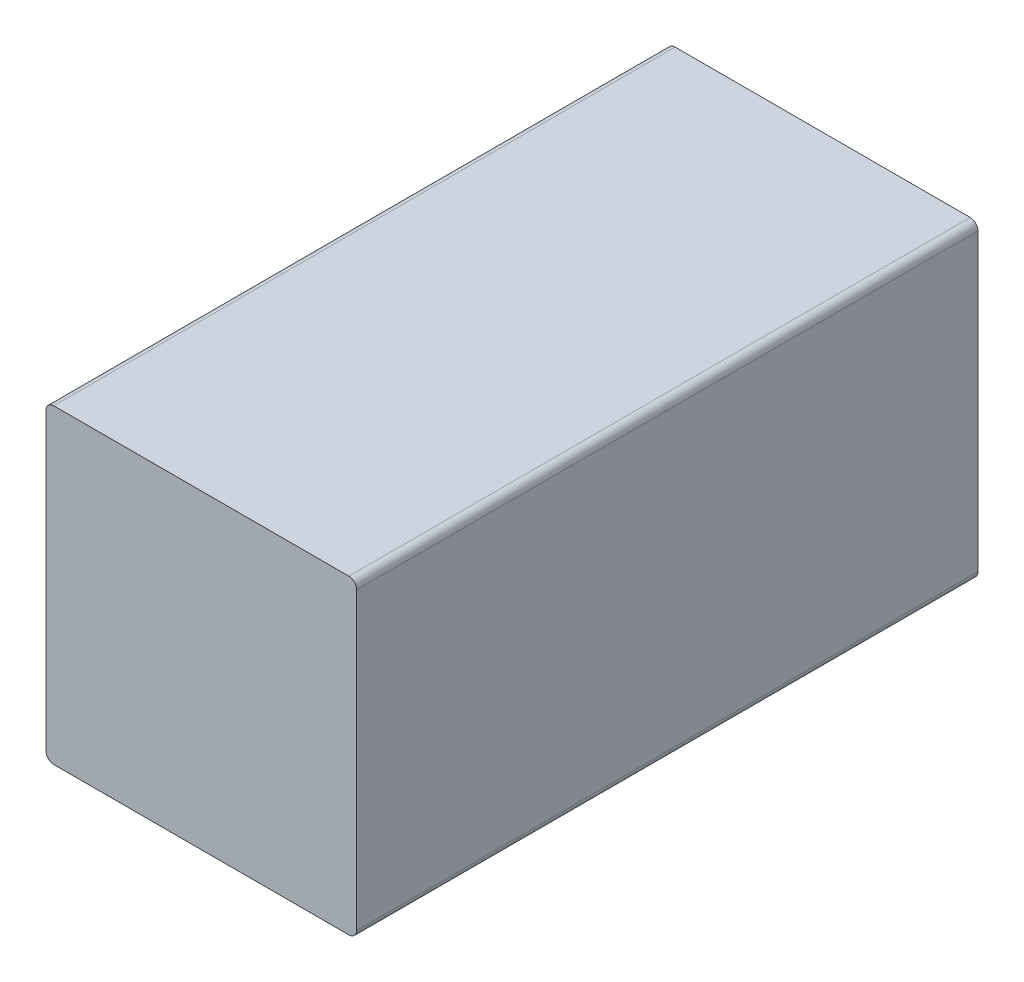
SolidWorks part; units mm, degrees
ref_plane "Front Plane" through (0, 0, 0) normal (0, 0, 1) x (1, 0, 0)
ref_plane "Top Plane" through (0, 0, 0) normal (0, 1, 0) x (1, 0, 0)
ref_plane "Right Plane" through (0, 0, 0) normal (1, 0, 0) x (0, 0, -1)
sketch "Sketch1" plane through (0, 0, 0) normal (1, 0, 0) x (0, 0, -1)
  line L0 (-4.7625, 2.3813) -> (4.7625, 2.3813)
  line L1 (-4.7625, 2.3813) -> (-4.7625, -2.3813) construction
  line L2 (0, 2.3813) -> (0, -2.3813) construction
  point P3 (-4.7625, 0)
  point P5 (0, 2.3813)
  point P6 (-7.1438, 2.3813)
  point P9 (7.1438, 2.3813)
  dimension "Length" = 9.525
  dimension "Height" = 4.7625
  dimension "D1" = 11.9062
sketch "Sketch2" plane through (0, 0, 0) normal (0, 0, 1) x (1, 0, 0)
  line L0 (-2.3813, 2.3813) -> (2.3813, 2.3813)
  line L1 (-2.3813, 2.3813) -> (-2.3813, -2.3813)
  line L2 (2.3813, 2.3813) -> (2.3813, -2.3813)
  line L3 (-2.3813, -2.3813) -> (2.3813, -2.3813)
  dimension "Width" = 4.7625
  dimension "Height" = 4.7625
sketch "Sketch3" plane through (0, 0, 0) normal (0, 0, 1) x (1, 0, 0)
  line L4 (2.3813, 2.3813) -> (-2.3813, 2.3813)
  line L5 (2.3813, -2.3813) -> (2.3813, 2.3813)
  line L6 (-2.3813, -2.3813) -> (2.3813, -2.3813)
  line L7 (-2.3813, 2.3813) -> (-2.3813, -2.3813)
  line L8 (2.3813, 2.3813) -> (-2.3813, 2.3813)
  line L9 (2.3813, -2.3813) -> (2.3813, 2.3813)
  line L10 (-2.3813, -2.3813) -> (2.3813, -2.3813)
  line L11 (-2.3813, 2.3813) -> (-2.3813, -2.3813)
  dimension "D1" = 0
extrude "Boss-Extrude1" add sketch "Sketch3" along normal up to vertex (4.7625 mm away) from vertex at -4.7625 starting at point (0, 2.3813, -4.7625)
fillet "Fillet1" radius 0.1191 4 edges at (2.3813, -2.3813, 0) (-2.3813, -2.3813, 0) (-2.3813, 2.3813, 0) (2.3813, 2.3813, 0)
equation "\"D1@Sketch1\"=\"Height@Sketch1\"*2.5"
equation "\"D1@Fillet1\"=\"Height@Sketch1\"*.025"
